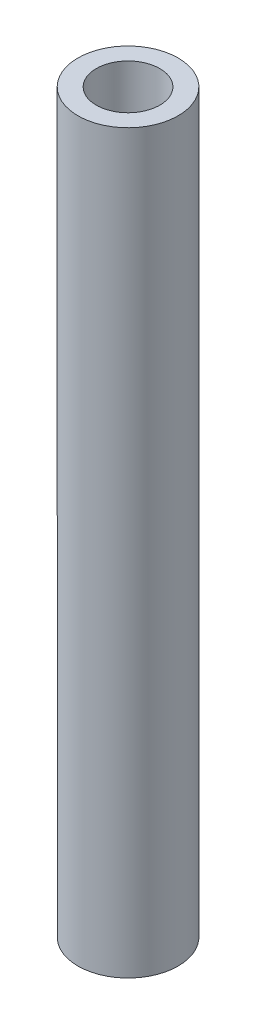
SolidWorks part; units mm, degrees
material "Cast Alloy Steel"
ref_plane "Front Plane" through (0, 0, 0) normal (0, 0, 1) x (1, 0, 0)
ref_plane "Top Plane" through (0, 0, 0) normal (0, 1, 0) x (1, 0, 0)
ref_plane "Right Plane" through (0, 0, 0) normal (1, 0, 0) x (0, 0, -1)
sketch "Sketch1" plane through (0, 0, 0) normal (0, 1, 0) x (1, 0, 0)
  circle A0 centre (0, 0) radius 4.7625
  circle A1 centre (0, 0) radius 3.019
  dimension "D1" = 9.525
extrude "Boss-Extrude1" add sketch "Sketch1" along normal mid plane 130
sketch "Sketch3" plane through (0, -65, 0) normal (0, -1, 0) x (1, 0, 0)
  circle A2 centre (0, 0) radius 4.7625
  circle A3 centre (0, 0) radius 4.7625
  dimension "D1" = 0
curve "Helix/Spiral1" pitch 2 height 320 turns 160
sketch "Sketch5" plane through (0, 0, 0) normal (1, 0, 0) x (0, 0, -1)
  line L0 (-3.019, -65) -> (3.019, -65) construction
  line L1 (15.559, 5) -> (-20.914, 5)
  line L2 (15.559, 5) -> (15.559, 86.3978)
  line L3 (15.559, 86.3978) -> (-20.914, 86.3978)
  line L4 (-20.914, 5) -> (-20.914, 86.3978)
  dimension "D1" = 70
extrude "Cut-Extrude2" cut sketch "Sketch5" against normal through all both and the other way through all
sketch "Sketch6" [suppressed] plane through (0, 0, 0) normal (1, 0, 0) x (0, 0, -1)
  line L0 (4.7625, 5) -> (-4.7625, 5) construction
  line L1 (-21.7865, -31) -> (15.4436, -31)
  line L2 (-21.7865, -31) -> (-21.7865, -75.0326)
  line L3 (-21.7865, -75.0326) -> (15.4436, -75.0326)
  line L4 (15.4436, -31) -> (15.4436, -75.0326)
  dimension "D1" = 36
extrude "Cut-Extrude3" [suppressed] cut sketch "Sketch6" against normal through all both and the other way through all
